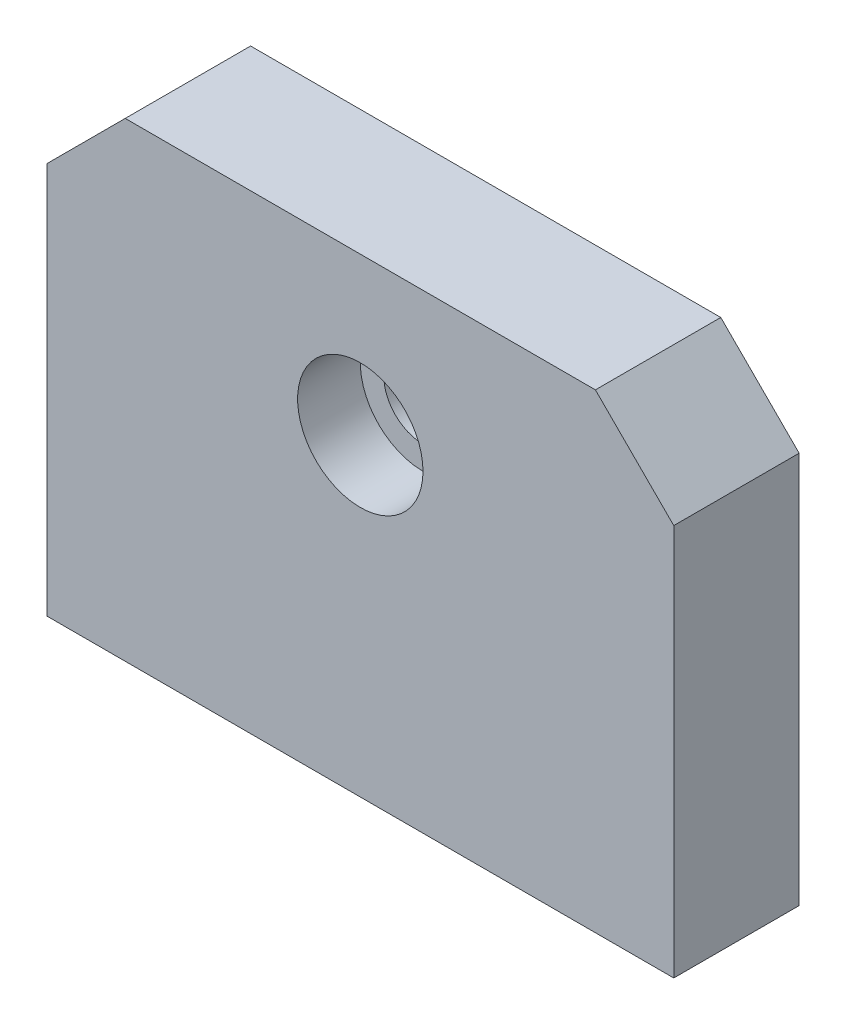
SolidWorks part; units mm, degrees
ref_plane "Plan de face" through (0, 0, 0) normal (0, 0, 1) x (1, 0, 0)
ref_plane "Plan de dessus" through (0, 0, 0) normal (0, 1, 0) x (1, 0, 0)
ref_plane "Plan de droite" through (0, 0, 0) normal (1, 0, 0) x (0, 0, -1)
sketch "Esquisse1" plane through (0, 0, 0) normal (0, 0, 1) x (1, 0, 0)
  line L0 (-20, -20) -> (-20, 5)
  line L2 (20, 5) -> (20, -20)
  line L3 (20, -20) -> (-20, -20)
  line L4 (-20, 5) -> (-15, 10)
  line L5 (-15, 10) -> (15, 10)
  line L6 (20, 5) -> (15, 10)
  circle A0 centre (0, 0) radius 2.5
extrude "Extrusion1" add sketch "Esquisse1" along normal blind 8
sketch "Esquisse2" plane through (0, 0, 8) normal (0, 0, 1) x (1, 0, 0)
  circle A0 centre (0, 0) radius 4
extrude "Extrusion2" cut sketch "Esquisse2" against normal blind 4
sketch "Esquisse3" plane through (0, -20, 0) normal (0, -1, 0) x (1, 0, 0)
  line L0 (-20, 8) -> (-20, 0) construction
  line L2 (-20, 4) -> (20, 4) construction
  line L4 (20, 8) -> (20, 0) construction
  circle A1 centre (-15.5, 4) radius 2
  circle A2 centre (15.5, 4) radius 2
extrude "Extrusion3" cut sketch "Esquisse3" against normal blind 15
